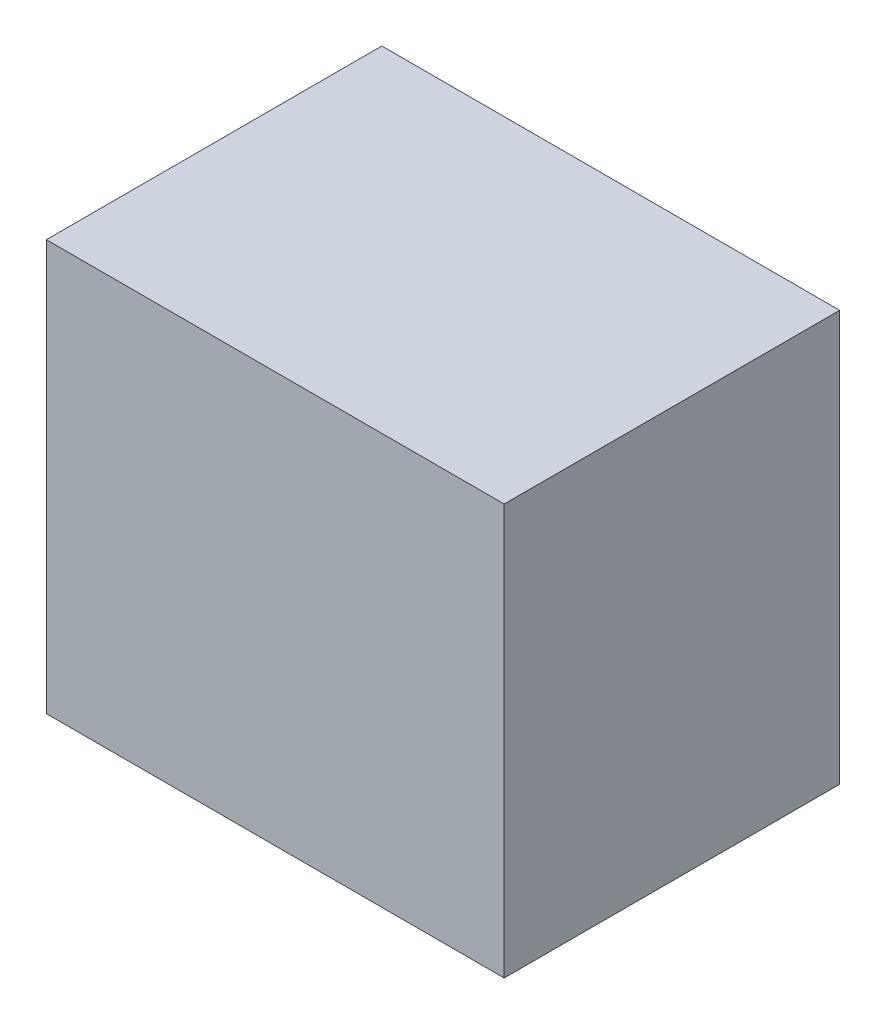
SolidWorks part; units mm, degrees
ref_plane "Front Plane" through (0, 0, 0) normal (0, 0, 1) x (1, 0, 0)
ref_plane "Top Plane" through (0, 0, 0) normal (0, 1, 0) x (1, 0, 0)
ref_plane "Right Plane" through (0, 0, 0) normal (1, 0, 0) x (0, 0, -1)
sketch "Sketch1" plane through (0, 0, 0) normal (0, 1, 0) x (1, 0, 0)
  line L1 (5.8, -4.25) -> (-5.8, -4.25)
  line L2 (5.8, -4.25) -> (5.8, 4.25)
  line L3 (5.8, 4.25) -> (-5.8, 4.25)
  line L4 (-5.8, -4.25) -> (-5.8, 4.25)
  line L5 (5.8, -4.25) -> (-5.8, 4.25) construction
  line L6 (5.8, 4.25) -> (-5.8, -4.25) construction
  point P0 (0, 0)
  dimension "D1" = 11.6
  dimension "D2" = 8.5
extrude "Boss-Extrude1" add sketch "Sketch1" along normal blind 10.4
